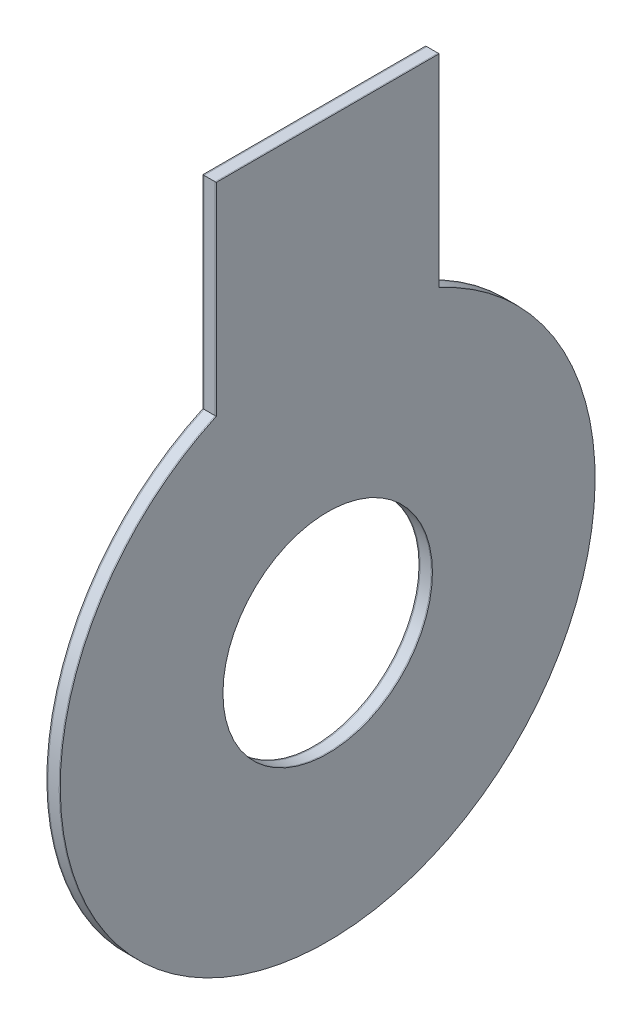
SolidWorks part; units mm, degrees
ref_plane "Front Plane" through (0, 0, 0) normal (0, 0, 1) x (1, 0, 0)
ref_plane "Top Plane" through (0, 0, 0) normal (0, 1, 0) x (1, 0, 0)
ref_plane "Right Plane" through (0, 0, 0) normal (1, 0, 0) x (0, 0, -1)
sketch "Sketch1" plane through (0, 0, 0) normal (1, 0, 0) x (0, 0, -1)
  line L0 (-25, 100) -> (25, 100)
  line L1 (-25, 100) -> (-25, 54.5436)
  line L2 (25, 100) -> (25, 54.5436)
  circle A0 centre (0, 0) radius 60
  circle A1 centre (0, 0) radius 23.5
  point P7 (0, 100)
  dimension "D1" = 120
  dimension "D2" = 47
  dimension "D3" = 40
  dimension "D4" = 50
extrude "Boss-Extrude1" add sketch "Sketch1" along normal blind 0.25 contours A0 L2 L0 L1 | A0 A1
sketch "Sketch4" plane through (0, 0, 0) normal (-1, 0, 0) x (0, 0, 1)
  line L3 (25, 54.5436) -> (25, 100)
  line L4 (25, 100) -> (-25, 100)
  line L5 (-25, 100) -> (-25, 54.5436)
  line L6 (25, 54.5436) -> (25, 100)
  line L7 (25, 100) -> (-25, 100)
  line L8 (-25, 100) -> (-25, 54.5436)
  circle A0 centre (0, 0) radius 23.5 construction
  arc A1 (-25, 54.5436) -> (25, 54.5436) centre (0, 0) ccw
  arc A2 (-25, 54.5436) -> (25, 54.5436) centre (0, 0) ccw
  circle A3 centre (0, 0) radius 23.5
  dimension "D1" = 0
extrude "Boss-Extrude4" add sketch "Sketch4" along normal blind 2.5 separate body
sketch "Sketch5" plane through (-2.5, 0, 0) normal (-1, 0, 0) x (0, 0, 1)
  line L3 (25, 54.5436) -> (25, 100)
  line L4 (25, 100) -> (-25, 100)
  line L5 (-25, 100) -> (-25, 54.5436)
  line L6 (25, 54.5436) -> (25, 100)
  line L7 (25, 100) -> (-25, 100)
  line L8 (-25, 100) -> (-25, 54.5436)
  circle A0 centre (0, 0) radius 23.5 construction
  arc A1 (-25, 54.5436) -> (25, 54.5436) centre (0, 0) ccw
  arc A2 (-25, 54.5436) -> (25, 54.5436) centre (0, 0) ccw
  circle A3 centre (0, 0) radius 23.5
  dimension "D1" = 0
extrude "Boss-Extrude5" add sketch "Sketch5" along normal blind 0.25 separate body contours A2 L6 L7 L8
